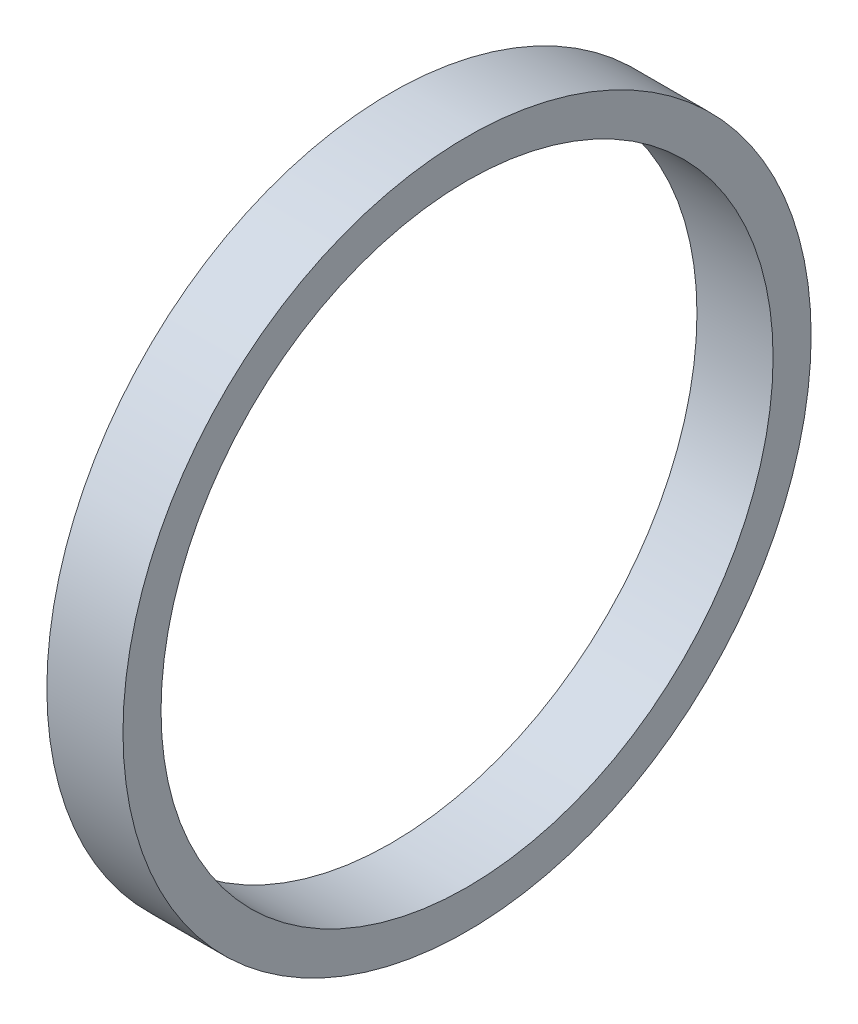
SolidWorks part; units mm, degrees
material "Brass"
ref_plane "Front Plane" through (0, 0, 0) normal (0, 0, 1) x (1, 0, 0)
ref_plane "Top Plane" through (0, 0, 0) normal (0, 1, 0) x (1, 0, 0)
ref_plane "Right Plane" through (0, 0, 0) normal (1, 0, 0) x (0, 0, -1)
sketch "Sketch1" plane through (0, 0, 0) normal (1, 0, 0) x (0, 0, -1)
  circle A0 centre (0, 0) radius 51.054
  circle A1 centre (0, 0) radius 57.404
  dimension "D1" = 102.108
  dimension "D2" = 114.808
extrude "Boss-Extrude1" add sketch "Sketch1" along normal mid plane 12.7
